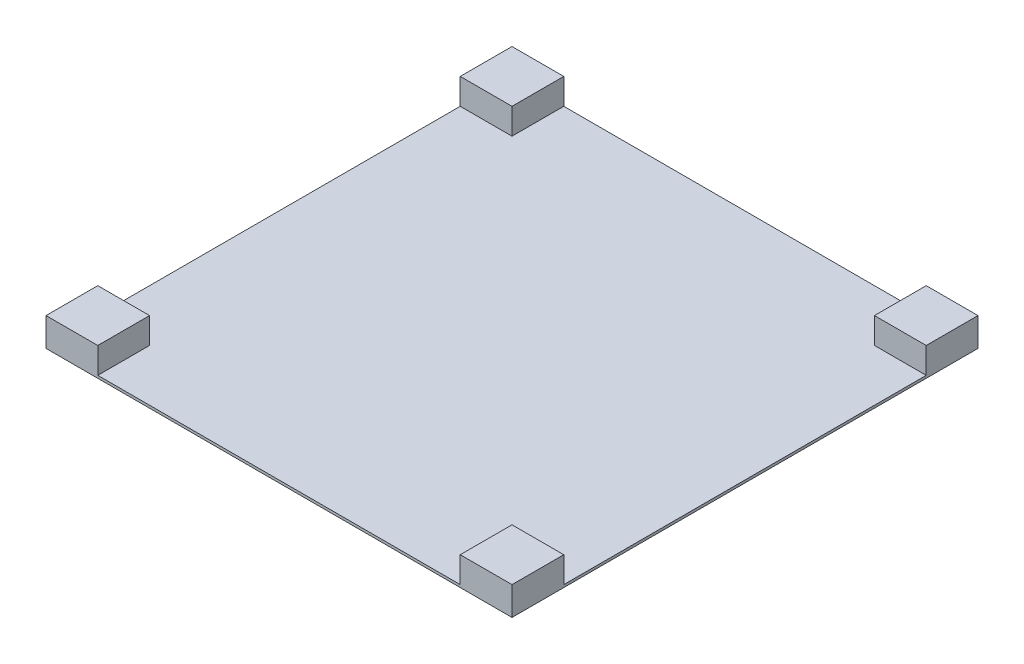
SolidWorks part; units mm, degrees
ref_plane "Front Plane" through (0, 0, 0) normal (0, 0, 1) x (1, 0, 0)
ref_plane "Top Plane" through (0, 0, 0) normal (0, 1, 0) x (1, 0, 0)
ref_plane "Right Plane" through (0, 0, 0) normal (1, 0, 0) x (0, 0, -1)
sketch "Sketch2" plane through (0, 0, 0) normal (0, 1, 0) x (1, 0, 0)
  line L1 (-450, 450) -> (450, 450)
  line L2 (-450, 450) -> (-450, -450)
  line L3 (-450, -450) -> (450, -450)
  line L4 (450, 450) -> (450, -450)
  line L5 (-450, 450) -> (450, -450) construction
  line L6 (-450, -450) -> (450, 450) construction
  point P0 (0, 0)
  dimension "D1" = 900
  dimension "D2" = 900
extrude "Boss-Extrude2" add sketch "Sketch2" along normal blind 5
sketch "Sketch4" plane through (0, 5, 0) normal (0, 1, 0) x (1, 0, 0)
  line L1 (-450, 450) -> (-350, 450)
  line L2 (-450, 450) -> (-450, 350)
  line L3 (-450, 350) -> (-350, 350)
  line L4 (-350, 450) -> (-350, 350)
  line L5 (-450, 450) -> (-350, 350) construction
  line L6 (-450, 350) -> (-350, 450) construction
  line L7 (350, 450) -> (450, 450)
  line L8 (350, 450) -> (350, 350)
  line L9 (350, 350) -> (450, 350)
  line L10 (450, 450) -> (450, 350)
  line L11 (350, 450) -> (450, 350) construction
  line L12 (350, 350) -> (450, 450) construction
  line L13 (350, -350) -> (450, -350)
  line L14 (350, -350) -> (350, -450)
  line L15 (350, -450) -> (450, -450)
  line L16 (450, -350) -> (450, -450)
  line L17 (350, -350) -> (450, -450) construction
  line L18 (350, -450) -> (450, -350) construction
  line L19 (-450, -350) -> (-350, -350)
  line L20 (-450, -350) -> (-450, -450)
  line L21 (-450, -450) -> (-350, -450)
  line L22 (-350, -350) -> (-350, -450)
  line L23 (-450, -350) -> (-350, -450) construction
  line L24 (-450, -450) -> (-350, -350) construction
  line L25 (450, 450) -> (-450, 450) construction
  line L26 (-450, 450) -> (-450, -450) construction
  line L27 (450, -450) -> (450, 450) construction
  line L28 (-450, -450) -> (450, -450) construction
  point P0 (-400, 400)
  point P5 (400, 400)
  point P10 (400, -400)
  point P15 (-400, -400)
  point P20 (0, 0)
  point P21 (0, 0)
  point P26 (450, 400)
  dimension "D1" = 100
extrude "Boss-Extrude3" add sketch "Sketch4" along normal blind 50
